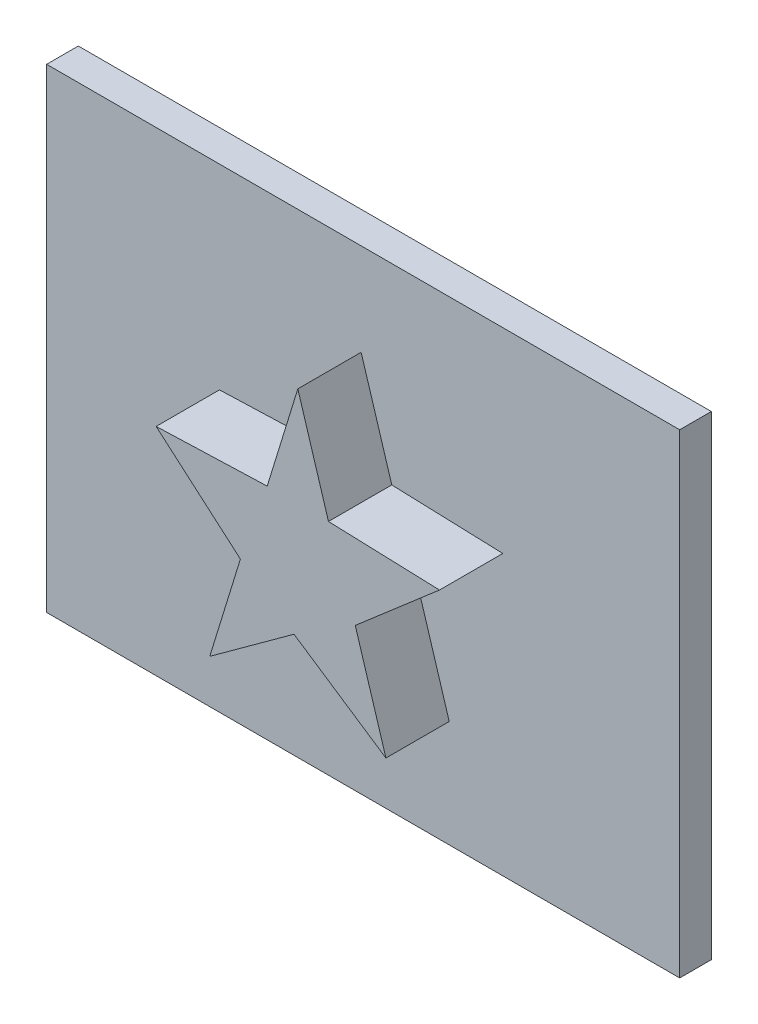
SolidWorks part; units mm, degrees
ref_plane "Front Plane" through (0, 0, 0) normal (0, 0, 1) x (1, 0, 0)
ref_plane "Top Plane" through (0, 0, 0) normal (0, 1, 0) x (1, 0, 0)
ref_plane "Right Plane" through (0, 0, 0) normal (1, 0, 0) x (0, 0, -1)
sketch "Sketch1" plane through (0, 0, 0) normal (0, 0, 1) x (1, 0, 0)
  line L1 (-20, 15) -> (20, 15)
  line L2 (-20, 15) -> (-20, -15)
  line L3 (-20, -15) -> (20, -15)
  line L4 (20, 15) -> (20, -15)
  line L5 (-20, 15) -> (20, -15) construction
  line L6 (-20, -15) -> (20, 15) construction
  point P0 (0, 0)
  dimension "D1" = 30
  dimension "D2" = 40
extrude "Boss-Extrude1" add sketch "Sketch1" along normal blind 2
sketch "Sketch2" plane through (0, 0, 2) normal (0, 0, 1) x (1, 0, 0)
  line L0 (-0.1287, 9.1755) -> (1.807, 2.8846)
  line L1 (1.807, 2.8846) -> (8.8238, 2.6426)
  line L2 (8.8238, 2.6426) -> (3.5007, -1.9546)
  line L3 (3.5007, -1.9546) -> (5.4364, -8.2455)
  line L4 (5.4364, -8.2455) -> (-0.3706, -4.3742)
  line L5 (-0.3706, -4.3742) -> (-5.6937, -8.2455)
  line L6 (-5.6937, -8.2455) -> (-3.7581, -1.9546)
  line L7 (-3.7581, -1.9546) -> (-9.0811, 2.6426)
  line L8 (-9.0811, 2.6426) -> (-2.0643, 2.8846)
  line L9 (-2.0643, 2.8846) -> (-0.1287, 9.1755)
extrude "Boss-Extrude2" add sketch "Sketch2" along normal blind 4
sketch "Orientation Sketch" plane through (0, 0, 2) normal (0, 0, 1) x (1, 0, 0)
  line L0 (-0.1287, 9.1755) -> (-2.0643, 2.8846) construction
  line L1 (1.807, 2.8846) -> (-0.1287, 9.1755) construction
  line L2 (8.8238, 2.6426) -> (1.807, 2.8846) construction
  line L3 (3.5007, -1.9546) -> (8.8238, 2.6426) construction
  line L4 (5.4364, -8.2455) -> (3.5007, -1.9546) construction
  line L5 (-0.3706, -4.3742) -> (5.4364, -8.2455) construction
  line L6 (-5.6937, -8.2455) -> (-0.3706, -4.3742) construction
  line L7 (-3.7581, -1.9546) -> (-5.6937, -8.2455) construction
  line L8 (-9.0811, 2.6426) -> (-3.7581, -1.9546) construction
  line L9 (-2.0643, 2.8846) -> (-9.0811, 2.6426) construction
  line L10 (20, -15) -> (20, 15) construction
  line L11 (20, 15) -> (-20, 15) construction
  line L12 (-20, 15) -> (-20, -15) construction
  line L13 (-20, -15) -> (20, -15) construction
  line L14 (-0.1287, 9.1755) -> (-2.0643, 2.8846)
  line L15 (1.807, 2.8846) -> (-0.1287, 9.1755)
  line L16 (8.8238, 2.6426) -> (1.807, 2.8846)
  line L17 (3.5007, -1.9546) -> (8.8238, 2.6426)
  line L18 (5.4364, -8.2455) -> (3.5007, -1.9546)
  line L19 (-0.3706, -4.3742) -> (5.4364, -8.2455)
  line L20 (-5.6937, -8.2455) -> (-0.3706, -4.3742)
  line L21 (-3.7581, -1.9546) -> (-5.6937, -8.2455)
  line L22 (-9.0811, 2.6426) -> (-3.7581, -1.9546)
  line L23 (-2.0643, 2.8846) -> (-9.0811, 2.6426)
  line L24 (20, -15) -> (20, 15) construction
  line L25 (20, 15) -> (-20, 15) construction
  line L26 (-20, 15) -> (-20, -15) construction
  line L27 (-20, -15) -> (20, -15) construction
  point P3 (0, 0)
other "FormTool1"
